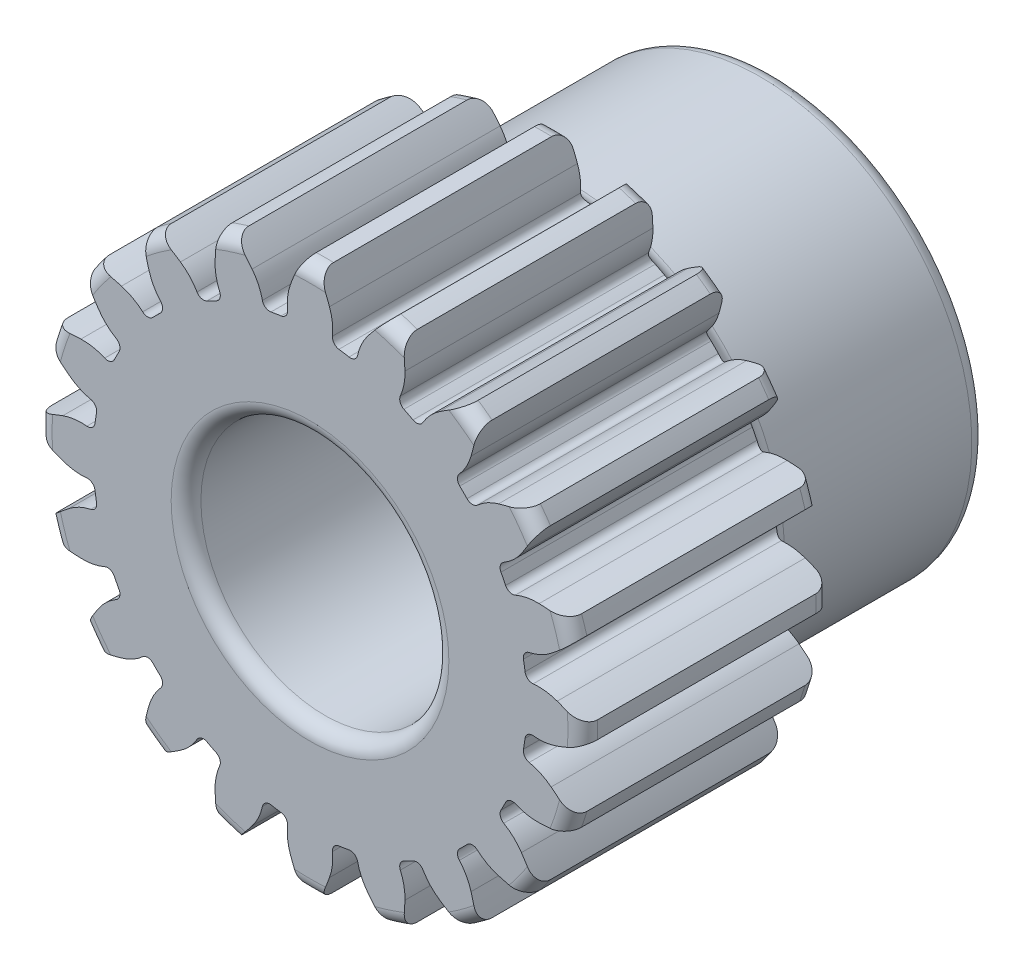
SolidWorks part; units mm, degrees
ref_plane "Front Plane" through (0, 0, 0) normal (0, 0, 1) x (1, 0, 0)
ref_plane "Top Plane" through (0, 0, 0) normal (0, 1, 0) x (1, 0, 0)
ref_plane "Right Plane" through (0, 0, 0) normal (1, 0, 0) x (0, 0, -1)
sketch "Sketch1" plane through (0, 0, 0) normal (0, 0, 1) x (1, 0, 0)
  line L0 (3.8225, 13.4469) -> (4.8115, 13.1256)
  line L1 (-13.97, 0) -> (13.97, 0) construction
  line L2 (0, 13.97) -> (0, 12.7) construction
  line L3 (0, 12.7) -> (0, 11.1125) construction
  line L4 (-0.5199, 13.97) -> (0.5199, 13.97)
  line L5 (-0.5199, 13.97) -> (-1.6022, 10.9964)
  line L6 (0.5199, 13.97) -> (1.6022, 10.9964)
  line L7 (3.8225, 13.4469) -> (1.8742, 10.9533)
  line L8 (-1.9949, -13.97) -> (1.9949, -13.97) construction
  line L9 (1.9949, -13.97) -> (0, -17.4253) construction
  line L10 (0, -17.4253) -> (-1.9949, -13.97) construction
  line L11 (0, -17.4253) -> (0, -17.2878) construction
  line L12 (-0.0794, -17.2878) -> (0.0794, -17.2878) construction
  line L13 (0, -14.1075) -> (0, -13.97) construction
  line L14 (4.317, 13.2863) -> (0, 0) construction
  line L15 (1.9155, -14.1075) -> (-1.9155, -14.1075) construction
  line L16 (4.8115, 13.1256) -> (4.9219, 9.9631)
  line L17 (-1.9552, -14.0387) -> (1.9552, -14.0387) construction
  line L18 (0, 0) -> (-1.1504, 11.4294) construction
  line L19 (0, 0) -> (2.4378, 11.2255) construction
  circle A0 centre (0, 0) radius 13.97
  circle A1 centre (0, 0) radius 12.7 construction
  circle A2 centre (0, 0) radius 6.35
  circle A3 centre (0, 0) radius 11.1125
  arc A4 (-0.9964, 12.6608) -> (0.9964, 12.6608) centre (0, 0) cw
  circle A5 centre (0, 0) radius 10.8331 construction
  arc A6 (-1.4788, 11.0137) -> (-1.1504, 11.4294) centre (-1.5295, 11.3913) ccw
  circle A8 centre (0, 0) radius 11.43 construction
  arc A10 (-0.9964, 12.6608) -> (-1.1504, 11.4294) centre (1.6206, 11.7083) ccw
  arc A11 (-0.4377, 13.97) -> (-0.9964, 12.6608) centre (11.3283, 8.175) ccw
  arc A13 (1.997, 10.9316) -> (2.4378, 11.2255) centre (2.0655, 11.3064) ccw
  arc A15 (2.9648, 12.3491) -> (2.4378, 11.2255) centre (5.1593, 10.6345) ccw
  arc A16 (3.9006, 13.4215) -> (2.9648, 12.3491) centre (13.3001, 4.2743) ccw
  arc A17 (1.4788, 11.0137) -> (1.1504, 11.4294) centre (1.5295, 11.3913) cw
  arc A18 (0.9964, 12.6608) -> (1.1504, 11.4294) centre (-1.6206, 11.7083) cw
  arc A19 (0.4377, 13.97) -> (0.9964, 12.6608) centre (-11.3283, 8.175) cw
  arc A20 (4.8098, 10.0177) -> (4.626, 10.5146) centre (4.9747, 10.3611) cw
  arc A21 (4.8601, 11.7333) -> (4.626, 10.5146) centre (2.0768, 11.6361) cw
  arc A22 (4.7333, 13.151) -> (4.8601, 11.7333) centre (-8.2476, 11.2755) cw
  point P5 (0, 13.97)
  point P8 (4.317, 13.2863)
  point P9 (8.2114, 11.302)
  point P10 (11.302, 8.2114)
  point P11 (13.2863, 4.317)
  point P12 (13.97, 0)
  point P13 (13.2863, -4.317)
  point P14 (11.302, -8.2114)
  point P15 (8.2114, -11.302)
  point P16 (4.317, -13.2863)
  point P17 (0, -13.97)
  point P18 (-4.317, -13.2863)
  point P19 (-8.2114, -11.302)
  point P20 (-11.302, -8.2114)
  point P21 (-13.2863, -4.317)
  point P22 (0, 0)
  point P37 (-1.9949, -13.97)
  point P47 (0, -14.0387)
  point P48 (61.8424, -13.97)
  point P49 (1.9949, -13.97)
  point P53 (5.9847, -13.97)
  point P54 (9.9746, -13.97)
  point P55 (13.9644, -13.97)
  point P56 (17.9542, -13.97)
  point P57 (21.9441, -13.97)
  point P58 (25.9339, -13.97)
  point P59 (29.9237, -13.97)
  point P60 (33.9136, -13.97)
  point P61 (37.9034, -13.97)
  point P62 (41.8932, -13.97)
  point P63 (45.8831, -13.97)
  point P64 (49.8729, -13.97)
  point P65 (53.8627, -13.97)
  point P66 (57.8526, -13.97)
  point P69 (65.8322, -13.97)
  point P70 (69.8221, -13.97)
  point P71 (73.8119, -13.97)
  point P81 (0, 10.8331)
  point P85 (-13.97, 0)
  point P86 (-13.2863, 4.317)
  point P87 (-11.302, 8.2114)
  point P89 (-8.2114, 11.302)
  point P90 (-4.317, 13.2863)
  dimension "OD" = 27.94
  dimension "Shaft Diameter" = 12.7
  dimension "Pitch Diameter" = 25.4
  dimension "Hub Diameter" = 21.6662
  dimension "D4" = 0.381
  dimension "Driven Dim* Addendum (a)" = 1.27
  dimension "Dedendum (b)" = 1.5875
  dimension "D2" = 3.9898
  dimension "D3" = 0.1588
  dimension "Pressure Angle" = 20
  dimension "Clearance" = 0.3175
  dimension "D5" = 18
  dimension "D1" = 1.9949
  dimension "Gear Pitch" = 20
  dimension "Teeth" = 20
sketch "Sketch2" plane through (0, 0, 0) normal (1, 0, 0) x (0, 0, -1)
  line L0 (-11.9126, 13.208) -> (-11.9126, -13.208)
  line L1 (-11.1506, -13.97) -> (0.0254, -13.97)
  line L2 (0.7874, -13.208) -> (0.7874, -11.5951)
  line L3 (1.5494, -10.8331) -> (11.1506, -10.8331)
  line L4 (11.9126, -10.0711) -> (11.9126, 10.0711)
  line L5 (11.1506, 10.8331) -> (1.5494, 10.8331)
  line L6 (0.7874, 11.5951) -> (0.7874, 13.208)
  line L7 (0.0254, 13.97) -> (-11.1506, 13.97)
  line L8 (11.9126, 0) -> (-11.9126, 0) construction
  line L10 (0.7874, 10.8331) -> (-11.9126, 10.8331) construction
  line L13 (11.9126, 6.35) -> (0, 6.35) construction
  line L15 (-11.9126, 6.35) -> (0, 6.35) construction
  line L17 (11.9126, -6.35) -> (0, -6.35) construction
  line L18 (0, -6.35) -> (-11.9126, -6.35) construction
  arc A0 (-11.9126, -13.208) -> (-11.1506, -13.97) centre (-11.1506, -13.208) ccw
  arc A1 (0.0254, -13.97) -> (0.7874, -13.208) centre (0.0254, -13.208) ccw
  arc A2 (0.7874, -11.5951) -> (1.5494, -10.8331) centre (1.5494, -11.5951) cw
  arc A3 (11.9126, -10.0711) -> (11.1506, -10.8331) centre (11.1506, -10.0711) cw
  arc A4 (0.7874, 11.5951) -> (1.5494, 10.8331) centre (1.5494, 11.5951) ccw
  arc A5 (-11.9126, 13.208) -> (-11.1506, 13.97) centre (-11.1506, 13.208) cw
  arc A6 (0.0254, 13.97) -> (0.7874, 13.208) centre (0.0254, 13.208) cw
  arc A7 (11.1506, 10.8331) -> (11.9126, 10.0711) centre (11.1506, 10.0711) cw
  point P40 (11.9126, 10.8331)
  dimension "Radius" = 0.762
  dimension "Hub Width" = 11.1252
  dimension "Overall Width" = 23.8252
sketch "Sketch3" plane through (0, 0, 0) normal (1, 0, 0) x (0, 0, -1)
  line L0 (11.1506, 6.35) -> (-11.1506, 6.35)
  line L1 (11.9126, -10.0711) -> (11.9126, 10.0711) construction
  line L2 (11.1506, 10.8331) -> (1.5494, 10.8331) construction
  line L3 (0.7874, 11.5951) -> (0.7874, 13.208) construction
  line L4 (0.0254, 13.97) -> (-11.1506, 13.97) construction
  line L5 (-11.9126, 13.208) -> (-11.9126, -13.208) construction
  line L6 (11.9126, 7.112) -> (11.9126, 10.0711)
  line L7 (11.1506, 10.8331) -> (1.5494, 10.8331)
  line L8 (0.7874, 11.5951) -> (0.7874, 13.208)
  line L9 (0.0254, 13.97) -> (-11.1506, 13.97)
  line L10 (-11.9126, 13.208) -> (-11.9126, 7.112)
  line L11 (11.9126, 6.35) -> (0, 6.35) construction
  arc A8 (11.9126, 10.0711) -> (11.1506, 10.8331) centre (11.1506, 10.0711) ccw construction
  arc A9 (0.7874, 11.5951) -> (1.5494, 10.8331) centre (1.5494, 11.5951) ccw construction
  arc A10 (0.7874, 13.208) -> (0.0254, 13.97) centre (0.0254, 13.208) ccw construction
  arc A11 (-11.1506, 13.97) -> (-11.9126, 13.208) centre (-11.1506, 13.208) ccw construction
  arc A12 (11.9126, 10.0711) -> (11.1506, 10.8331) centre (11.1506, 10.0711) ccw
  arc A13 (0.7874, 11.5951) -> (1.5494, 10.8331) centre (1.5494, 11.5951) ccw
  arc A14 (0.7874, 13.208) -> (0.0254, 13.97) centre (0.0254, 13.208) ccw
  arc A15 (-11.1506, 13.97) -> (-11.9126, 13.208) centre (-11.1506, 13.208) ccw
  arc A16 (-11.9126, 7.112) -> (-11.1506, 6.35) centre (-11.1506, 7.112) ccw
  arc A17 (11.1506, 6.35) -> (11.9126, 7.112) centre (11.1506, 7.112) ccw
revolve "Revolve1" add sketch "Sketch3" angle 360 about L8
sketch "Sketch4" plane through (0, 0, 11.9126) normal (0, 0, 1) x (1, 0, 0)
  circle A9 centre (0, 0) radius 13.97 construction
  circle A21 centre (0, 0) radius 11.1125 construction
  arc A22 (1.997, 10.9316) -> (2.4378, 11.2255) centre (2.0655, 11.3064) ccw construction
  arc A23 (2.9648, 12.3491) -> (2.4378, 11.2255) centre (5.1593, 10.6345) ccw construction
  arc A24 (3.9006, 13.4215) -> (2.9648, 12.3491) centre (13.3001, 4.2743) ccw construction
  arc A25 (0.9964, 12.6608) -> (0.4377, 13.97) centre (-11.3283, 8.175) ccw construction
  arc A26 (1.1504, 11.4294) -> (0.9964, 12.6608) centre (-1.6206, 11.7083) ccw construction
  arc A27 (1.1504, 11.4294) -> (1.4788, 11.0137) centre (1.5295, 11.3913) ccw construction
  arc A28 (3.8952, 13.416) -> (0.4412, 13.963) centre (0, 0) ccw
  arc A29 (1.997, 10.9316) -> (1.4788, 11.0137) centre (0, 0) ccw
  arc A30 (1.997, 10.9316) -> (2.4378, 11.2255) centre (2.0655, 11.3064) ccw
  arc A31 (2.9648, 12.3491) -> (2.4378, 11.2255) centre (5.1593, 10.6345) ccw
  arc A32 (3.8952, 13.416) -> (2.9648, 12.3491) centre (13.3001, 4.2743) ccw
  arc A33 (0.9964, 12.6608) -> (0.4412, 13.963) centre (-11.3283, 8.175) ccw
  arc A34 (1.1504, 11.4294) -> (0.9964, 12.6608) centre (-1.6206, 11.7083) ccw
  arc A35 (1.1504, 11.4294) -> (1.4788, 11.0137) centre (1.5295, 11.3913) ccw
extrude "Cut-Extrude1" cut sketch "Sketch4" against normal through all both and the other way through all
pattern_circular "CirPattern1" count 20 every 18 about axis through (0, 0, 0) along (0, 0, 1) of "Cut-Extrude1"
equation "\"D3@Sketch1\"=(1/\"Gear Pitch@Sketch1\")/8"
equation "\"D2@Sketch1\"=3.1416/\"Gear Pitch@Sketch1\""
equation "\"Dedendum (b)@Sketch1\"=1.25/\"Gear Pitch@Sketch1\""
equation "\"D1@Sketch1\"=1.5708/\"Gear Pitch@Sketch1\""
equation "\"D4@Sketch1\"=.3/\"Gear Pitch@Sketch1\""
equation "\"Clearance@Sketch1\" = .25 / \"Gear Pitch@Sketch1\""
equation "\"D1@CirPattern1\"=\"Teeth@Sketch1\""
equation "\"D5@Sketch1\"=360/\"Teeth@Sketch1\""
equation "\"D2@CirPattern1\"=\"D5@Sketch1\""
equation "\"Radius@Sketch2\"=.6/\"Gear Pitch@Sketch1\""
